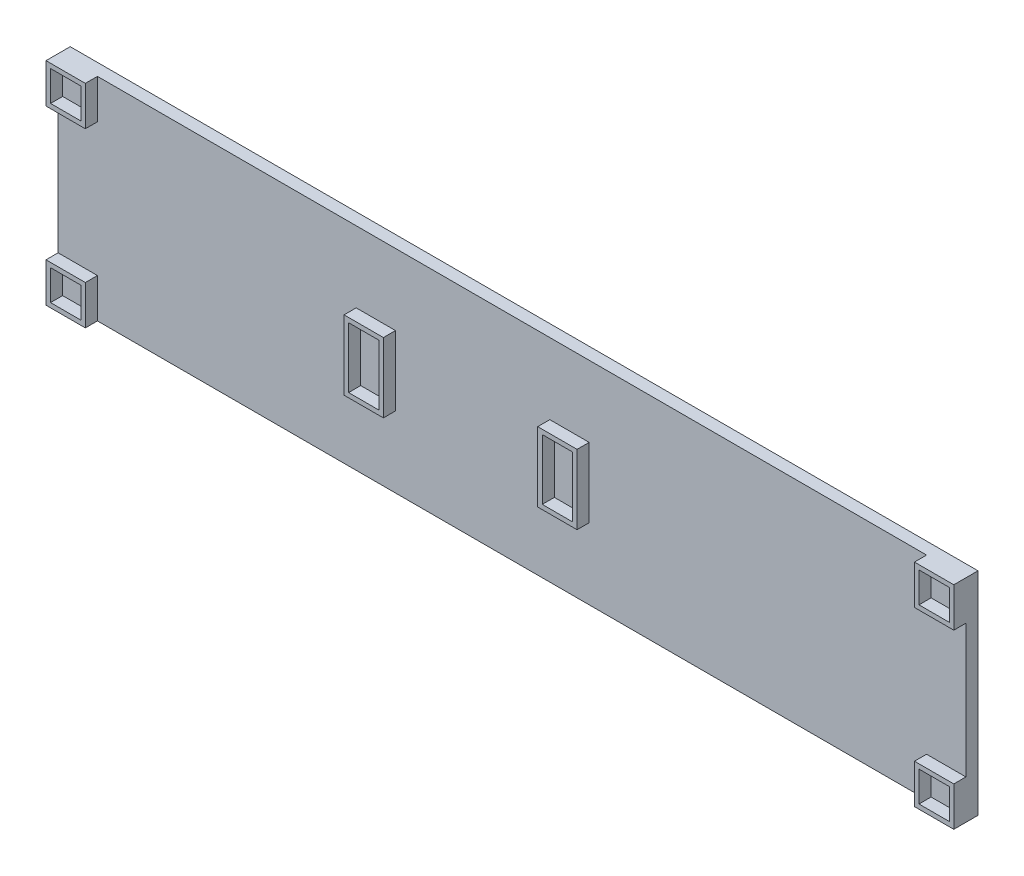
SolidWorks part; units mm, degrees
ref_plane "Přední rovina" through (0, 0, 0) normal (0, 0, 1) x (1, 0, 0)
ref_plane "Horní rovina" through (0, 0, 0) normal (0, 1, 0) x (1, 0, 0)
ref_plane "Pravá rovina" through (0, 0, 0) normal (1, 0, 0) x (0, 0, -1)
sketch "Skica1" plane through (0, 0, 0) normal (0, 0, 1) x (1, 0, 0)
  line L1 (75, 17.5) -> (-75, 17.5)
  line L2 (75, 17.5) -> (75, -17.5)
  line L3 (75, -17.5) -> (-75, -17.5)
  line L4 (-75, 17.5) -> (-75, -17.5)
  line L5 (75, 17.5) -> (-75, -17.5) construction
  line L6 (75, -17.5) -> (-75, 17.5) construction
  point P0 (0, 0)
  point P5 (-27.5, 0)
  point P11 (4.5, 0)
  dimension "D1" = 35
  dimension "D2" = 150
extrude "Přidat vysunutím2" add sketch "Skica1" along normal blind 2 contours L2 L1 L4 L3
sketch "Skica2" plane through (0, 0, 2) normal (0, 0, 1) x (1, 0, 0)
  line L0 (-75, 17.5) -> (-75, -17.5) construction
  line L1 (-25, 5) -> (-20, 5)
  line L2 (-25, 5) -> (-25, -5)
  line L3 (-25, -5) -> (-20, -5)
  line L4 (-20, 5) -> (-20, -5)
  line L5 (-25, 5) -> (-20, -5) construction
  line L6 (-25, -5) -> (-20, 5) construction
  line L8 (12, 5) -> (7, 5)
  line L9 (12, 5) -> (12, -5)
  line L10 (12, -5) -> (7, -5)
  line L11 (7, 5) -> (7, -5)
  line L12 (12, 5) -> (7, -5) construction
  line L13 (12, -5) -> (7, 5) construction
  line L14 (-25.75, 5.75) -> (-19.25, 5.75)
  line L15 (-25.75, 5.75) -> (-25.75, -5.75)
  line L16 (-25.75, -5.75) -> (-19.25, -5.75)
  line L17 (-19.25, 5.75) -> (-19.25, -5.75)
  line L18 (-25.75, 5.75) -> (-19.25, -5.75) construction
  line L19 (-25.75, -5.75) -> (-19.25, 5.75) construction
  line L20 (6.25, 5.75) -> (12.75, 5.75)
  line L21 (6.25, 5.75) -> (6.25, -5.75)
  line L22 (6.25, -5.75) -> (12.75, -5.75)
  line L23 (12.75, 5.75) -> (12.75, -5.75)
  line L24 (6.25, 5.75) -> (12.75, -5.75) construction
  line L25 (6.25, -5.75) -> (12.75, 5.75) construction
  point P0 (-22.5, 0)
  point P7 (9.5, 0)
  point P12 (-22.5, 0)
  point P17 (9.5, 0)
  dimension "D1" = 10
  dimension "D2" = 5
  dimension "D3" = 50
  dimension "D4" = 10
  dimension "D5" = 5
  dimension "D6" = 27
  dimension "D7" = 11.5
  dimension "D8" = 6.5
  dimension "D9" = 11.5
  dimension "D10" = 6.5
extrude "Přidat vysunutím3" add sketch "Skica2" along normal blind 2
sketch "Skica3" plane through (0, 0, 2) normal (0, 0, 1) x (1, 0, 0)
  line L0 (75, 17.5) -> (-75, 17.5) construction
  line L1 (-75, 17.5) -> (-68.5, 17.5)
  line L2 (-75, 17.5) -> (-75, 11)
  line L3 (-75, 11) -> (-68.5, 11)
  line L4 (-68.5, 17.5) -> (-68.5, 11)
  line L5 (-75, 17.5) -> (-68.5, 11) construction
  line L6 (-75, 11) -> (-68.5, 17.5) construction
  line L7 (-75, 17.5) -> (-75, -17.5) construction
  line L8 (69.25, 16.75) -> (74.25, 11.75) construction
  line L9 (-74.25, 16.75) -> (-69.25, 16.75)
  line L10 (-74.25, 16.75) -> (-74.25, 11.75)
  line L11 (-74.25, 11.75) -> (-69.25, 11.75)
  line L12 (-69.25, 16.75) -> (-69.25, 11.75)
  line L13 (-74.25, 16.75) -> (-69.25, 11.75) construction
  line L14 (-74.25, 11.75) -> (-69.25, 16.75) construction
  line L15 (69.25, 11.75) -> (74.25, 16.75) construction
  line L16 (69.25, 16.75) -> (69.25, 11.75)
  line L17 (69.25, 16.75) -> (74.25, 16.75)
  line L18 (74.25, 16.75) -> (74.25, 11.75)
  line L19 (69.25, 11.75) -> (74.25, 11.75)
  line L20 (68.5, 17.5) -> (68.5, 11)
  line L21 (68.5, 17.5) -> (75, 17.5)
  line L22 (75, 17.5) -> (75, 11)
  line L23 (68.5, 11) -> (75, 11)
  line L24 (-74.25, -11.75) -> (-74.25, -16.75)
  line L25 (-74.25, -11.75) -> (-69.25, -11.75)
  line L26 (-69.25, -11.75) -> (-69.25, -16.75)
  line L27 (-74.25, -16.75) -> (-69.25, -16.75)
  line L28 (-75, -11) -> (-75, -17.5)
  line L29 (-75, -11) -> (-68.5, -11)
  line L30 (-68.5, -11) -> (-68.5, -17.5)
  line L31 (-75, -17.5) -> (-68.5, -17.5)
  line L32 (69.25, -11.75) -> (69.25, -16.75)
  line L33 (69.25, -16.75) -> (74.25, -16.75)
  line L34 (74.25, -11.75) -> (74.25, -16.75)
  line L35 (69.25, -11.75) -> (74.25, -11.75)
  line L36 (68.5, -11) -> (68.5, -17.5)
  line L37 (68.5, -17.5) -> (75, -17.5)
  line L38 (75, -11) -> (75, -17.5)
  line L39 (68.5, -11) -> (75, -11)
  point P0 (-71.75, 14.25)
  point P9 (-71.75, 14.25)
  point P20 (71.75, 14.25)
  dimension "D1" = 6.5
  dimension "D2" = 6.5
  dimension "D3" = 0
  dimension "D4" = 0
  dimension "D5" = 5
  dimension "D6" = 2
  dimension "D7" = 2
extrude "Přidat vysunutím4" add sketch "Skica3" along normal blind 2
